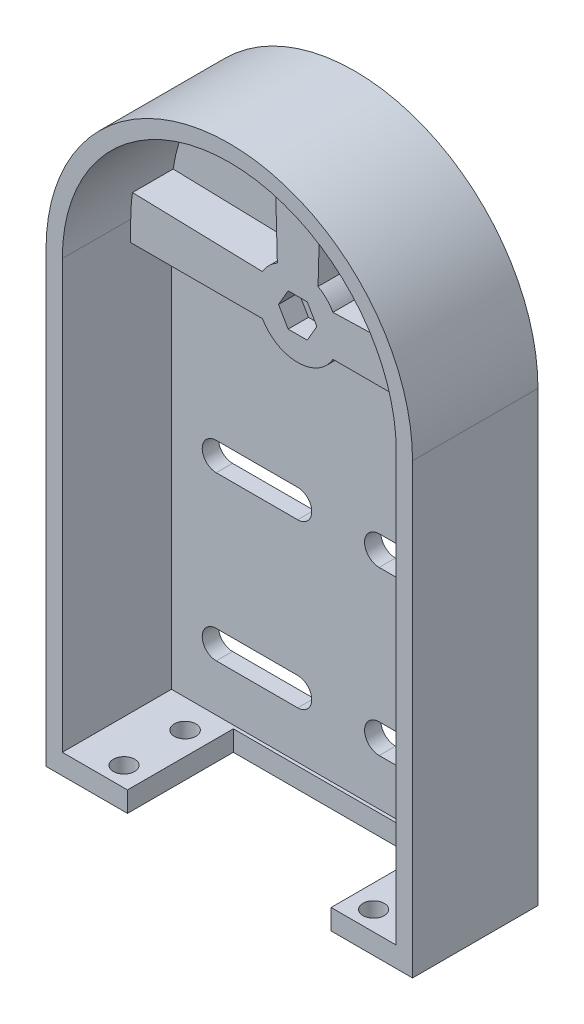
SolidWorks part; units mm, degrees
ref_plane "Alzado" through (0, 0, 0) normal (0, 0, 1) x (1, 0, 0)
ref_plane "Planta" through (0, 0, 0) normal (0, 1, 0) x (1, 0, 0)
ref_plane "Vista lateral" through (0, 0, 0) normal (1, 0, 0) x (0, 0, -1)
sketch "Croquis1" plane through (0, 0, 0) normal (0, 0, 1) x (1, 0, 0)
  line L0 (0, 0) -> (0, 110) construction
  line L1 (-41, 0) -> (41, 0)
  line L2 (-41, 0) -> (-41, 110)
  line L3 (41, 0) -> (41, 110)
  arc A0 (41, 110) -> (-41, 110) centre (0, 110) ccw
  dimension "D3" = 82
  dimension "D1" = 110
  dimension "D2" = 41
extrude "Saliente-Extruir1" add sketch "Croquis1" along normal blind 4
sketch "Croquis2" plane through (0, 0, 4) normal (0, 0, 1) x (1, 0, 0)
  line L0 (0, 110) -> (0, 112.75) construction
  line L1 (0, 110) -> (-5, 110) construction
  line L2 (-8.6603, 105) -> (-41, 105)
  line L3 (0, 110) -> (-5, 110) construction
  line L6 (0, 110) -> (5, 110) construction
  line L7 (0, 110) -> (0, 112.75) construction
  line L12 (0, 110) -> (5, 110) construction
  line L14 (8.6603, 105) -> (41, 105)
  line L15 (-41, 110) -> (-41, 0) construction
  line L16 (41, 0) -> (41, 110) construction
  line L17 (-41, 110) -> (-41, 105)
  line L18 (41, 105) -> (41, 110)
  line L19 (-10, 110) -> (-41, 110) construction
  line L20 (-10, 110) -> (-41, 110) construction
  line L21 (-8.6603, 115) -> (-40.5795, 115.8571)
  line L22 (-5, 118.6603) -> (-5.8571, 150.5795)
  line L23 (0, 120) -> (0, 151) construction
  line L24 (0, 120) -> (0, 151) construction
  line L25 (5, 118.6603) -> (5.8571, 150.5795)
  line L26 (8.6603, 115) -> (40.5795, 115.8571)
  line L27 (10, 110) -> (41, 110) construction
  line L28 (10, 110) -> (41, 110) construction
  circle A0 centre (0, 110) radius 2.75
  circle A1 centre (0, 110) radius 10
  arc A2 (41, 110) -> (-41, 110) centre (0, 110) ccw construction
  arc A4 (5.8571, 150.5795) -> (-5.8571, 150.5795) centre (0, 110) ccw
  arc A6 (-40.5795, 115.8571) -> (-41, 110) centre (0, 110) ccw
  arc A9 (41, 110) -> (40.5795, 115.8571) centre (0, 110) ccw
  point P3 (-17.5, 110)
  point P11 (0, 127.5)
  point P22 (17.5, 110)
  dimension "D1" = 5.5
  dimension "D3" = 20
extrude "Saliente-Extruir2" add sketch "Croquis2" along normal blind 10
sketch "Croquis3" plane through (0, 0, 0) normal (0, 0, -1) x (-1, 0, 0)
  line L0 (-41, 0) -> (-41, 110) construction
  line L1 (41, 110) -> (41, 0) construction
  line L2 (-41, 0) -> (-41, 110)
  line L3 (-45, 0) -> (-41, 0)
  line L4 (41, 110) -> (41, 0)
  line L5 (41, 0) -> (45, 0)
  line L6 (45, -4) -> (45, 110)
  line L7 (-45, 110) -> (-45, -4)
  line L8 (-45, -4) -> (45, -4)
  line L9 (45, 0) -> (45, 110)
  line L10 (-45, 110) -> (-45, 0)
  arc A0 (41, 110) -> (-41, 110) centre (0, 110) ccw construction
  arc A1 (41, 110) -> (-41, 110) centre (0, 110) ccw
  arc A2 (45, 110) -> (-45, 110) centre (0, 110) ccw
  arc A3 (45, 110) -> (-45, 110) centre (0, 110) ccw
  dimension "D1" = 4
extrude "Saliente-Extruir3" add sketch "Croquis3" against normal blind 30.8
sketch "Croquis4" plane through (0, 0, 4) normal (0, 0, 1) x (1, 0, 0)
  circle A0 centre (0, 110) radius 2.75
extrude "Cortar-Extruir1" cut sketch "Croquis4" against normal up to surface (4 mm away) up to face at (0, 66.25, 0)
hole_wizard "Refrentado para tornillo tapón con cabeza plana de clavija de M52" positions "Croquis3D2" profile "Croquis6" countersink size "M5" standard "Ansi Metric" end condition through all
sketch3d "Croquis3D2"
  line L0 (0, 110, 14) -> (0, 110, 0) construction
  point P0 (0, 110, 0)
sketch "Croquis6" plane through (0, 110, 0) normal (1, 0, 0) x (0, 1, 0)
  line L0 (0, 0) -> (0, 30.8)
  line L1 (0, 30.8) -> (2.75, 30.8)
  line L2 (2.75, 30.8) -> (2.75, 2.85)
  line L3 (2.75, 2.85) -> (5.6, 0)
  line L5 (5.6, 0) -> (0, 0)
  line L6 (-2.75, 2.85) -> (-5.6, 0) construction
  line L11 (0, -6.35) -> (0, 107.95) construction
  dimension "Diámetro de taladro hasta el siguiente" = 5.5
  dimension "Profundidad de taladro hasta el siguiente" = 30.8
  dimension "Diámetro de avellanado cercano" = 11.2
  dimension "Ángulo de avellanado cercano" = 90
sketch "Croquis7" plane through (0, 0, 0) normal (0, 0, -1) x (-1, 0, 0)
  line L1 (2.1893, 105.8349) -> (4.7017, 109.8134)
  line L2 (4.7017, 109.8134) -> (2.5124, 113.9785)
  line L3 (2.5124, 113.9785) -> (-2.1893, 114.1651)
  line L4 (-2.1893, 114.1651) -> (-4.7017, 110.1866)
  line L5 (-4.7017, 110.1866) -> (-2.5124, 106.0215)
  line L6 (-2.5124, 106.0215) -> (2.1893, 105.8349)
  circle A0 centre (0, 110) radius 4.075 construction
  dimension "D1" = 8.15
extrude "Cortar-Extruir2" cut sketch "Croquis7" against normal blind 5
sketch "Croquis8" plane through (0, 0, 14) normal (0, 0, 1) x (1, 0, 0)
  line L1 (4.7054, 110) -> (2.3527, 114.075)
  line L2 (2.3527, 114.075) -> (-2.3527, 114.075)
  line L3 (-2.3527, 114.075) -> (-4.7054, 110)
  line L4 (-4.7054, 110) -> (-2.3527, 105.925)
  line L5 (-2.3527, 105.925) -> (2.3527, 105.925)
  line L6 (2.3527, 105.925) -> (4.7054, 110)
  circle A0 centre (0, 110) radius 4.075 construction
  dimension "D1" = 8.15
extrude "Cortar-Extruir3" cut sketch "Croquis8" against normal blind 5
sketch "Croquis9" plane through (0, 0, 14) normal (0, 0, 1) x (1, 0, 0)
  line L0 (-20, 110) -> (-20, 60) construction
  line L1 (0, 110) -> (0, 63.2723) construction
  line L2 (20, 110) -> (20, 60) construction
  line L3 (-30, 60) -> (-10, 60) construction
  line L4 (-30, 63.4488) -> (-10, 63.4488)
  line L5 (-30, 56.5512) -> (-10, 56.5512)
  line L6 (10, 60) -> (30, 60) construction
  line L7 (10, 63.5806) -> (30, 63.5806)
  line L8 (10, 56.4194) -> (30, 56.4194)
  line L9 (-41, 40) -> (38.2275, 40) construction
  line L10 (-41, 105) -> (-41, 0) construction
  line L11 (-30, 20) -> (-10, 20) construction
  line L12 (-30, 16.5512) -> (-10, 16.5512)
  line L13 (-30, 23.4488) -> (-10, 23.4488)
  line L14 (10, 20) -> (30, 20) construction
  line L15 (10, 16.4194) -> (30, 16.4194)
  line L16 (10, 23.5806) -> (30, 23.5806)
  arc A1 (-30, 63.4488) -> (-30, 56.5512) centre (-30, 60) ccw
  arc A2 (-10, 56.5512) -> (-10, 63.4488) centre (-10, 60) ccw
  arc A3 (10, 63.5806) -> (10, 56.4194) centre (10, 60) ccw
  arc A4 (30, 56.4194) -> (30, 63.5806) centre (30, 60) ccw
  arc A5 (-30, 16.5512) -> (-30, 23.4488) centre (-30, 20) cw
  arc A6 (-10, 23.4488) -> (-10, 16.5512) centre (-10, 20) cw
  arc A7 (10, 16.4194) -> (10, 23.5806) centre (10, 20) cw
  arc A8 (30, 23.5806) -> (30, 16.4194) centre (30, 20) cw
  point P11 (-20, 60)
  point P18 (20, 60)
  point P29 (-20, 20)
  point P36 (20, 20)
  dimension "D2" = 20
  dimension "D3" = 50
  dimension "D4" = 20
  dimension "D5" = 20
extrude "Cortar-Extruir4" cut sketch "Croquis9" against normal up to surface (14 mm away) up to face at (-5.6, 110, 0)
ref_plane "Plano1" through (0, 5, 0) normal (0, -1, 0) x (-1, 0, 0)
sketch "Croquis10" plane through (0, 5, 0) normal (0, -1, 0) x (-1, 0, 0)
  line L1 (41, -4) -> (-41, -4)
  line L2 (41, -4) -> (41, -30.8)
  line L3 (41, -30.8) -> (-41, -30.8)
  line L4 (-41, -4) -> (-41, -30.8)
extrude "Saliente-Extruir4" add sketch "Croquis10" along normal up to surface (5 mm away) up to face at (0, 0, 16.4)
sketch "Croquis11" plane through (0, 0, 0) normal (0, -1, 0) x (1, 0, 0)
  line L0 (0, 0) -> (0, 4) construction
  line L1 (-35, 4.8) -> (-25, 4.8)
  line L3 (-35, 30.8) -> (-25, 30.8)
  line L4 (-35, 30.8) -> (-35, 4.8)
  line L5 (25, 4.8) -> (35, 4.8)
  line L6 (35, 30.8) -> (35, 4.8)
  line L7 (45, 30.8) -> (-45, 30.8) construction
  line L8 (-25, 30.8) -> (-25, 4.8)
  line L9 (0, 0) -> (0, 30.8) construction
  line L10 (25, 30.8) -> (25, 4.8)
  line L11 (35, 30.8) -> (25, 30.8)
  line L12 (35, 30.8) -> (35, 4.8)
  line L13 (-45, 0) -> (45, 0) construction
  line L15 (-25, 4.8) -> (25, 4.8)
  line L16 (-25, 4.8) -> (-25, 30.8)
  line L17 (-25, 30.8) -> (25, 30.8)
  line L18 (25, 4.8) -> (25, 30.8)
  circle A0 centre (-30.65, 11) radius 2.6552
  circle A1 centre (-30.65, 26) radius 2.6197
  circle A2 centre (30.65, 11) radius 2.6552
  circle A3 centre (30.65, 26) radius 2.6197
  point P5 (0, 17)
  line M3 (45, 30.8) -> (-45, 30.8)
  dimension "D1" = 11
  dimension "D2" = 70
  dimension "D3" = 10
  dimension "D4" = 26
  dimension "D5" = 4.35
  dimension "D6" = 15
extrude "Cortar-Extruir5" cut sketch "Croquis11" against normal up to surface (5 mm away) contours A1 | L8 L15 L10 M3 | A3 | A2 | A0 up to face at (0, 5, 17.4)
